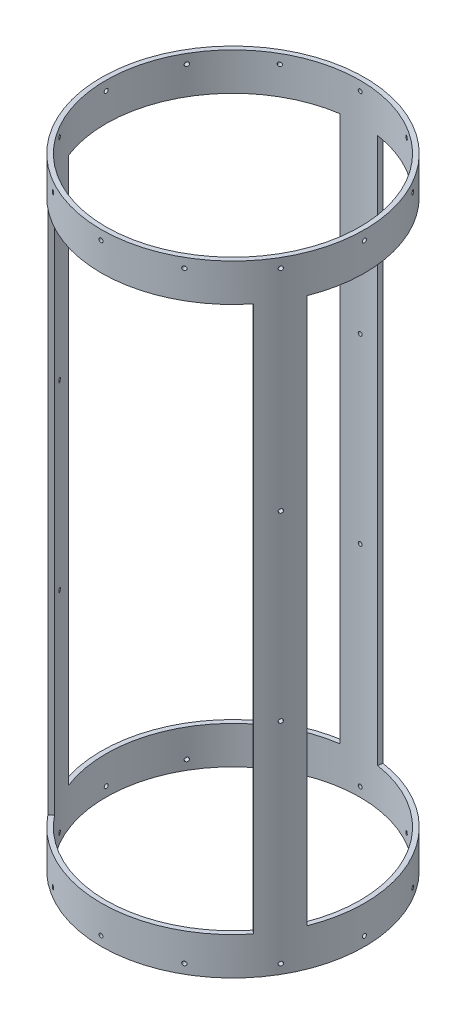
SolidWorks part; units mm, degrees
material "6061-T6 (SS)"
ref_plane "Front Plane" through (0, 0, 0) normal (0, 0, 1) x (1, 0, 0)
ref_plane "Top Plane" through (0, 0, 0) normal (0, 1, 0) x (1, 0, 0)
ref_plane "Right Plane" through (0, 0, 0) normal (1, 0, 0) x (0, 0, -1)
sketch "Sketch1" plane through (0, 0, 0) normal (0, 1, 0) x (1, 0, 0)
  circle A0 centre (0, 0) radius 88.9
  circle A1 centre (0, 0) radius 85.725
  dimension "D1" = 177.8
  dimension "D2" = 171.45
extrude "Boss-Extrude1" add sketch "Sketch1" along normal mid plane 419.1
sketch "Sketch6" plane through (0, -209.55, 0) normal (0, -1, 0) x (-1, 0, 0)
  line L0 (82.7901, -32.3885) -> (79.8333, -31.2317)
  line L1 (13.1222, 87.9262) -> (12.6536, 84.786)
  line L2 (0, 0) -> (0, 85.725) construction
  line L3 (-97.8543, 0) -> (97.8543, 0) construction
  line L4 (0, 0) -> (12.6536, 84.786) construction
  arc A0 (13.1222, 87.9262) -> (82.7901, -32.3885) centre (0, 0) cw
  circle A1 centre (0, 0) radius 88.9 construction
  arc A2 (12.6536, 84.786) -> (79.8333, -31.2317) centre (0, 0) cw
  circle A3 centre (0, 0) radius 85.725 construction
  arc A4 (0, 85.725) -> (12.6536, 84.786) centre (0, 0) cw construction
  dimension "D1" = 153.924
  dimension "D2" = 12.7
extrude "Cut-Extrude5" cut sketch "Sketch6" against normal offset from surface (368.3 mm away) 25.4 from offset 25.4 up to face at (0, 209.55, 88.9) offset against normal yes
pattern_circular "CirPattern5" count 3 over 360 about axis through (0, 0, 0) along (0, 1, 0) of "Cut-Extrude5"
ref_plane "Plane1" through (0, 0, -88.9) normal (0, 0, -1) x (-1, 0, 0)
sketch "Sketch3" plane through (0, 0, 0) normal (0, 0, -1) x (-1, 0, 0)
  line L1 (-88.9, -209.55) -> (88.9, -209.55) construction
  line L3 (-12.8692, 184.15) -> (-12.8692, -184.15) construction
  circle A0 centre (-0.1692, -203.2) radius 1.3525
  dimension "D1" = 6.35
  dimension "D2" = 2.7051
  dimension "D4" = 12.7
extrude "Cut-Extrude2" cut sketch "Sketch3" along normal up to surface (88.8921 mm away)
pattern_circular "CirPattern2" count 12 over 360 about axis through (0, 209.55, 0) along (0, -1, 0) of "Cut-Extrude2"
sketch "Sketch4" plane through (0, 0, -88.9) normal (0, 0, -1) x (-1, 0, 0)
  line L1 (88.9, 209.55) -> (-88.9, 209.55) construction
  circle A0 centre (-0.1692, 203.2) radius 1.3525
  dimension "D1" = 2.7051
  dimension "D2" = 6.35
extrude "Cut-Extrude3" cut sketch "Sketch4" against normal blind 15.24
pattern_circular "CirPattern3" count 12 over 360 about axis through (0, 209.55, 0) along (0, 1, 0) of "Cut-Extrude3"
ref_plane "Plane2" through (0, 0, 88.9) normal (0, 0, 1) x (1, 0, 0)
sketch "Sketch5" plane through (0, 0, 88.9) normal (0, 0, 1) x (1, 0, 0)
  line L0 (-88.9, 184.15) -> (-13.1222, 184.15) construction
  line L1 (88.9, -184.15) -> (13.3458, -184.15) construction
  circle A0 centre (0.1692, 61.3833) radius 1.3526
  circle A1 centre (0.1692, -61.3833) radius 1.3526
  dimension "D1" = 122.7667
  dimension "D2" = 122.7667
  dimension "D3" = 2.7051
  dimension "D4" = 2.7051
extrude "Cut-Extrude4" cut sketch "Sketch5" against normal up to surface (177.787 mm away)
pattern_circular "CirPattern4" count 3 over 360 about axis through (0, 209.55, 0) along (0, -1, 0) of "Cut-Extrude4"
